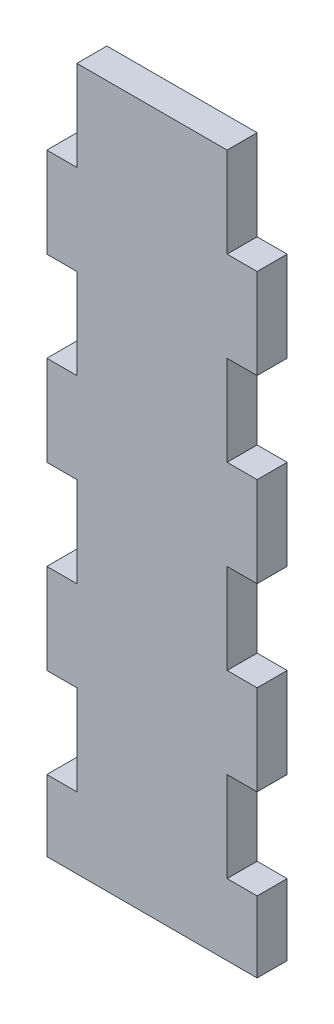
SolidWorks part; units mm, degrees
ref_plane "Front Plane" through (0, 0, 0) normal (0, 0, 1) x (1, 0, 0)
ref_plane "Top Plane" through (0, 0, 0) normal (0, 1, 0) x (1, 0, 0)
ref_plane "Right Plane" through (0, 0, 0) normal (1, 0, 0) x (0, 0, -1)
sketch "Model" plane through (0, 0, 0) normal (0, 0, 1) x (1, 0, 0)
  line L0 (16.8841, 128.0217) -> (22.8841, 128.0217)
  line L1 (22.8841, 110.0217) -> (16.8841, 110.0217)
  line L2 (16.8841, 92.0217) -> (22.8841, 92.0217)
  line L3 (22.8841, 74.0217) -> (16.8841, 74.0217)
  line L4 (16.8841, 56.0217) -> (22.8841, 56.0217)
  line L5 (22.8841, 38.0217) -> (16.8841, 38.0217)
  line L6 (58.8841, 128.0217) -> (52.8841, 128.0217)
  line L7 (52.8841, 110.0217) -> (58.8841, 110.0217)
  line L8 (58.8841, 92.0217) -> (52.8841, 92.0217)
  line L9 (52.8841, 74.0217) -> (58.8841, 74.0217)
  line L10 (58.8841, 56.0217) -> (52.8841, 56.0217)
  line L11 (52.8841, 38.0217) -> (58.8841, 38.0217)
  line L12 (58.8841, 128.0217) -> (58.8841, 110.0217)
  line L13 (58.8841, 92.0217) -> (58.8841, 74.0217)
  line L14 (58.8841, 56.0217) -> (58.8841, 38.0217)
  line L15 (16.8841, 128.0217) -> (16.8841, 110.0217)
  line L16 (16.8841, 92.0217) -> (16.8841, 74.0217)
  line L17 (16.8841, 56.0217) -> (16.8841, 38.0217)
  line L18 (22.8841, 146.0217) -> (22.8841, 128.0217)
  line L19 (22.8841, 110.0217) -> (22.8841, 92.0217)
  line L20 (22.8841, 74.0217) -> (22.8841, 56.0217)
  line L21 (22.8841, 38.0217) -> (22.8841, 20.0217)
  line L22 (52.8841, 20.0217) -> (52.8841, 38.0217)
  line L23 (52.8841, 56.0217) -> (52.8841, 74.0217)
  line L24 (52.8841, 92.0217) -> (52.8841, 110.0217)
  line L25 (52.8841, 128.0217) -> (52.8841, 146.0217)
  line L26 (52.8841, 20.0217) -> (58.8841, 20.0217)
  line L27 (58.8841, 20.0217) -> (58.8841, 5.8294)
  line L28 (16.8841, 20.0217) -> (16.8841, 5.8294)
  line L29 (22.8841, 20.0217) -> (16.8841, 20.0217)
  line L30 (22.8841, 146.0217) -> (52.8841, 146.0217)
  line L31 (16.8841, 5.8294) -> (58.8841, 5.8294)
extrude "Boss-Extrude1" add sketch "Model" along normal blind 6 contours L19 L2 L16 L3 L20 L4 L17 L5 L21 L29 L28 L31 L27 L26 L22 L11 L14 L10 L23 L9 L13 L8 L24 L7 L12 L6 L25 L30 L18 L0 L15 L1
